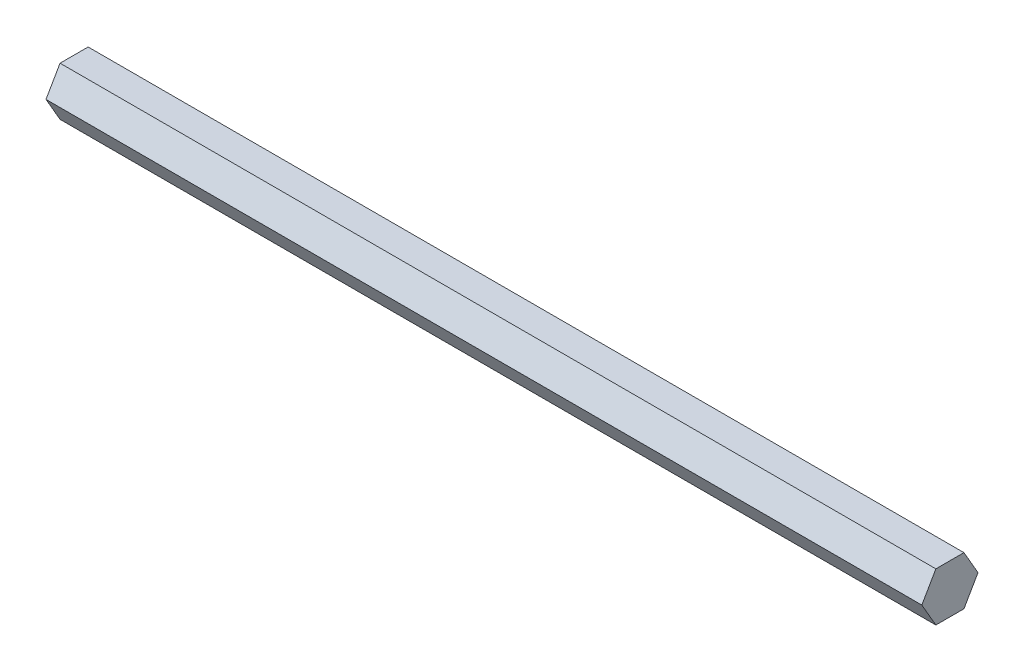
SolidWorks part; units mm, degrees
ref_plane "Front Plane" through (0, 0, 0) normal (0, 0, 1) x (1, 0, 0)
ref_plane "Top Plane" through (0, 0, 0) normal (0, 1, 0) x (1, 0, 0)
ref_plane "Right Plane" through (0, 0, 0) normal (1, 0, 0) x (0, 0, -1)
ref_plane "Plane1" through (0, 0, 0) normal (-1, 0, 0) x (0, -1, 0)
sketch "Sketch1" plane through (0, 0, 0) normal (-1, 0, 0) x (0, -1, 0)
  line L0 (-6.35, 3.6662) -> (-6.35, -3.6662)
  line L1 (-6.35, -3.6662) -> (0, -7.3323)
  line L2 (0, -7.3323) -> (6.35, -3.6662)
  line L3 (6.35, -3.6662) -> (6.35, 3.6662)
  line L4 (6.35, 3.6662) -> (0, 7.3323)
  line L5 (0, 7.3323) -> (-6.35, 3.6662)
extrude "Boss-Extrude1" add sketch "Sketch1" against normal blind 228.6
